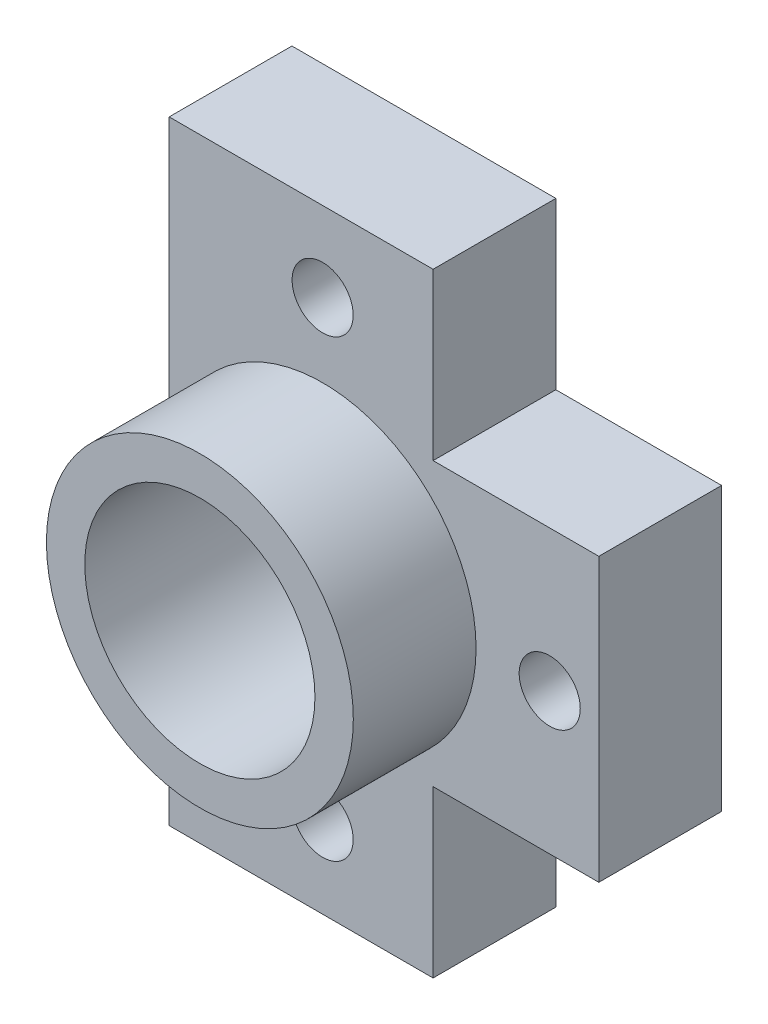
SolidWorks part; units mm, degrees
ref_plane "Front Plane" through (0, 0, 0) normal (0, 0, 1) x (1, 0, 0)
ref_plane "Top Plane" through (0, 0, 0) normal (0, 1, 0) x (1, 0, 0)
ref_plane "Right Plane" through (0, 0, 0) normal (1, 0, 0) x (0, 0, -1)
sketch "Sketch1" plane through (0, 0, 0) normal (0, 0, 1) x (1, 0, 0)
  line L1 (-8.89, -12.7) -> (8.89, -12.7)
  line L2 (-8.89, -12.7) -> (-8.89, 12.7)
  line L3 (-8.89, 12.7) -> (8.89, 12.7)
  line L4 (8.89, -12.7) -> (8.89, 12.7)
  line L5 (-8.89, -12.7) -> (8.89, 12.7) construction
  line L6 (-8.89, 12.7) -> (8.89, -12.7) construction
  point P0 (0, 0)
extrude "Extrude1" add sketch "Sketch1" along normal blind 10.16
sketch "Sketch4" plane through (0, 0, 10.16) normal (0, 0, 1) x (1, 0, 0)
  line L0 (-2.54, 0) -> (-2.54, -9.398) construction
  line L2 (-2.54, 0) -> (-2.54, 9.398) construction
  line L4 (-2.54, 0) -> (6.858, 0) construction
  line L7 (-8.89, 0) -> (-2.54, 0) construction
  line L8 (-8.89, 12.7) -> (-8.89, -12.7) construction
hole_wizard "3/8 (0.375) Diameter Hole1" positions "3DSketch4" profile "Sketch9" hole size "3/8" standard "Ansi Inch"
sketch3d "3DSketch4"
  point P0 (-2.54, 0, 10.16)
sketch "Sketch9" plane through (-2.54, 0, 10.16) normal (1, 0, 0) x (0, -1, 0)
  line L0 (0, 0) -> (0, 15.5616)
  line L1 (0, 15.5616) -> (4.7625, 12.7)
  line L2 (4.7625, 12.7) -> (4.7625, 0)
  line L5 (4.7625, 0) -> (0, 0)
  line L10 (0, 15.5616) -> (-4.7625, 12.7) construction
  line L11 (0, -6.35) -> (0, 107.95) construction
  dimension "Hole Dia." = 9.525
  dimension "Hole Depth" = 12.7
  dimension "Drill Angle" = 118
sketch "Sketch11" plane through (0, 0, 10.16) normal (0, 0, 1) x (1, 0, 0)
  circle A0 centre (-2.54, 0) radius 6.35
extrude "Extrude3" cut sketch "Sketch11" against normal blind 5.08 flip side to cut
hole_wizard "#39 (0.0995) Diameter Hole1" positions "3DSketch5" profile "Sketch13" hole size "#39" standard "Ansi Inch" end condition through all
sketch3d "3DSketch5"
  point P0 (6.858, 0, 10.16)
  point P3 (-2.54, -9.398, 10.16)
  point P6 (-2.54, 9.398, 10.16)
sketch "Sketch13" plane through (6.858, 0, 10.16) normal (1, 0, 0) x (0, -1, 0)
  line L0 (0, 0) -> (0, 10.16)
  line L1 (0, 10.16) -> (1.2636, 10.16)
  line L2 (1.2636, 10.16) -> (1.2636, 0)
  line L5 (1.2636, 0) -> (0, 0)
  line L11 (0, -6.35) -> (0, 107.95) construction
  dimension "Thru Hole Dia." = 2.5273
  dimension "Thru Hole Depth" = 10.16
sketch "Sketch14" plane through (0, 0, 5.08) normal (0, 0, 1) x (1, 0, 0)
  line L1 (8.89, 12.7) -> (2.032, 12.7)
  line L2 (8.89, 12.7) -> (8.89, 5.842)
  line L3 (8.89, 5.842) -> (2.032, 5.842)
  line L4 (2.032, 12.7) -> (2.032, 5.842)
  line L5 (8.89, -12.7) -> (2.032, -12.7)
  line L6 (8.89, -12.7) -> (8.89, -5.842)
  line L7 (8.89, -5.842) -> (2.032, -5.842)
  line L8 (2.032, -12.7) -> (2.032, -5.842)
extrude "Extrude4" cut sketch "Sketch14" against normal through all
